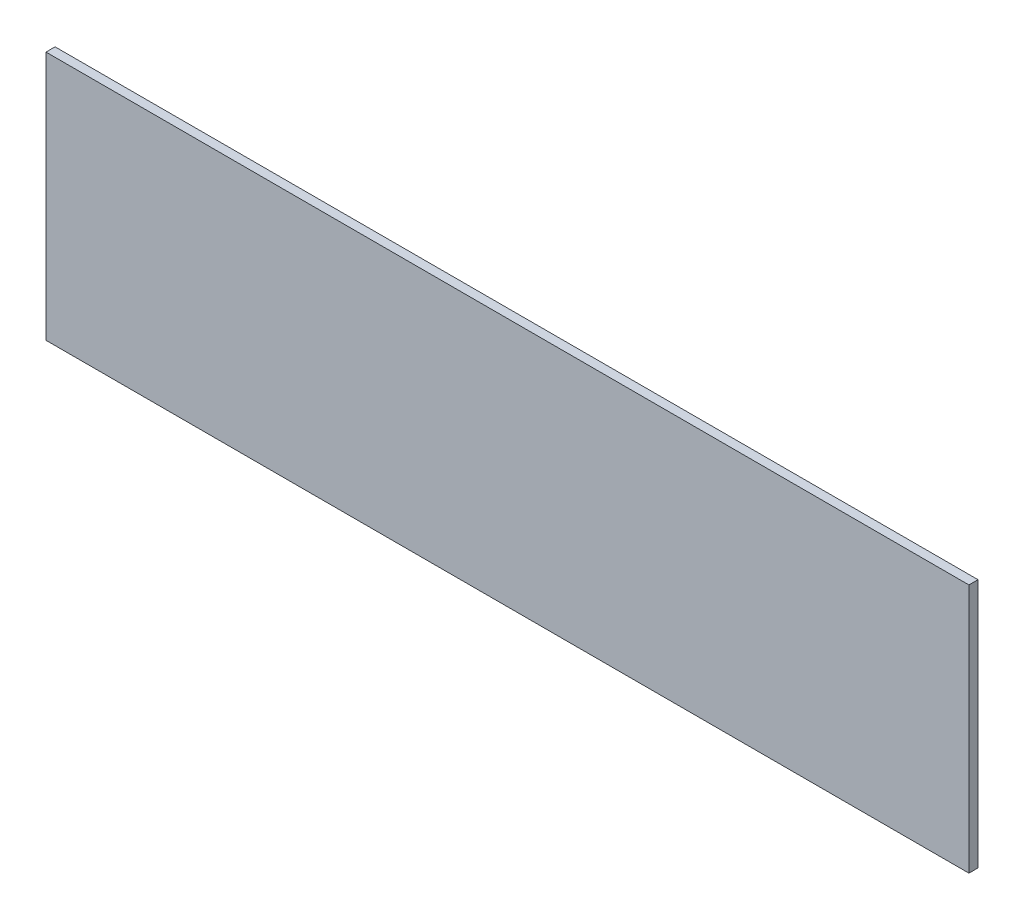
SolidWorks part; units mm, degrees
material "Acrílico (Impacto medio-alto)"
ref_plane "Alzado" through (0, 0, 0) normal (0, 0, 1) x (1, 0, 0)
ref_plane "Planta" through (0, 0, 0) normal (0, 1, 0) x (1, 0, 0)
ref_plane "Vista lateral" through (0, 0, 0) normal (1, 0, 0) x (0, 0, -1)
sketch "Croquis1" plane through (0, 0, 0) normal (0, 0, 1) x (1, 0, 0)
  line L1 (0, 0) -> (305, 0)
  line L2 (0, 0) -> (0, 82.5)
  line L3 (0, 82.5) -> (305, 82.5)
  line L4 (305, 0) -> (305, 82.5)
  dimension "D1" = 82.5
  dimension "D2" = 305
extrude "Saliente-Extruir1" add sketch "Croquis1" along normal blind 3
